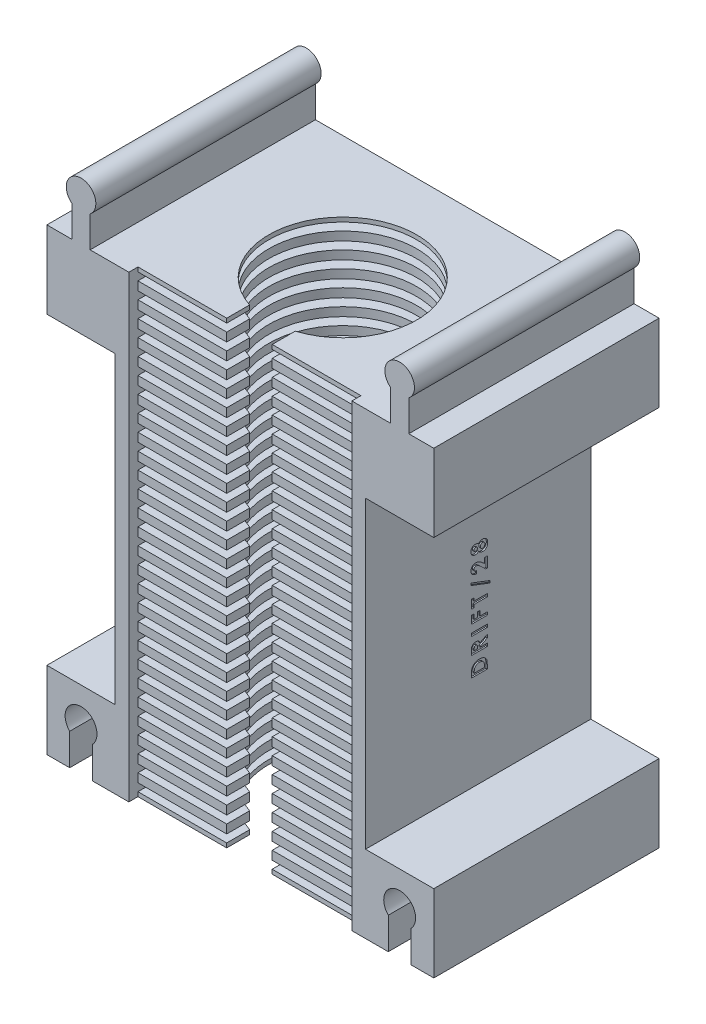
SolidWorks part; units mm, degrees
ref_plane "Plan de face" through (0, 0, 0) normal (0, 0, 1) x (1, 0, 0)
ref_plane "Plan de dessus" through (0, 0, 0) normal (0, 1, 0) x (1, 0, 0)
ref_plane "Plan de droite" through (0, 0, 0) normal (1, 0, 0) x (0, 0, -1)
sketch "Esquisse1" plane through (0, 0, 0) normal (0, 0, 1) x (1, 0, 0)
  line L1 (-20.1477, 24.3067) -> (34.8523, 24.3067)
  line L2 (-20.1477, 24.3067) -> (-20.1477, -85.1933)
  line L3 (-20.1477, -85.1933) -> (34.8523, -85.1933)
  line L4 (34.8523, 24.3067) -> (34.8523, -85.1933)
  dimension "D1" = 55
  dimension "D2" = 109.5
extrude "Boss.-Extru.2" add sketch "Esquisse1" along normal blind 49.5
sketch "Esquisse6" plane through (0, 0, 49.5) normal (0, 0, 1) x (1, 0, 0)
  line L0 (-20.1477, -85.1933) -> (34.8523, -85.1933) construction
  line L1 (-17.1477, 17.5067) -> (31.8523, 17.5067)
  line L2 (-17.1477, 17.5067) -> (-17.1477, -85.1933)
  line L3 (-17.1477, -85.1933) -> (31.8523, -85.1933)
  line L4 (31.8523, 17.5067) -> (31.8523, -85.1933)
  line L5 (-20.1477, 24.3067) -> (-20.1477, -85.1933) construction
  dimension "D1" = 49
  dimension "D2" = 3
  dimension "D3" = 102.7
extrude "Enlèv. mat.-Extru.2" cut sketch "Esquisse6" against normal blind 47
sketch "Esquisse7" plane through (0, 0, 2.5) normal (0, 0, 1) x (1, 0, 0)
  line L0 (31.8523, -85.1933) -> (31.8523, 17.5067) construction
  line L1 (-17.1477, -85.1933) -> (31.8523, -85.1933)
  line L2 (-17.1477, -85.1933) -> (-17.1477, -83.2933)
  line L3 (-17.1477, -83.2933) -> (31.8523, -83.2933)
  line L4 (31.8523, -85.1933) -> (31.8523, -83.2933)
  line L5 (-17.1477, -81.5933) -> (-17.1477, -79.6933)
  line L6 (-17.1477, -81.5933) -> (31.8523, -81.5933)
  line L7 (31.8523, -81.5933) -> (31.8523, -79.6933)
  line L8 (-17.1477, -79.6933) -> (31.8523, -79.6933)
  line L9 (-17.1477, -77.9933) -> (-17.1477, -76.0933)
  line L10 (-17.1477, -77.9933) -> (31.8523, -77.9933)
  line L11 (31.8523, -77.9933) -> (31.8523, -76.0933)
  line L12 (-17.1477, -76.0933) -> (31.8523, -76.0933)
  line L13 (-17.1477, -74.3933) -> (-17.1477, -72.4933)
  line L14 (-17.1477, -74.3933) -> (31.8523, -74.3933)
  line L15 (31.8523, -74.3933) -> (31.8523, -72.4933)
  line L16 (-17.1477, -72.4933) -> (31.8523, -72.4933)
  line L17 (-17.1477, -70.7933) -> (-17.1477, -68.8933)
  line L18 (-17.1477, -70.7933) -> (31.8523, -70.7933)
  line L19 (31.8523, -70.7933) -> (31.8523, -68.8933)
  line L20 (-17.1477, -68.8933) -> (31.8523, -68.8933)
  line L21 (-17.1477, -67.1933) -> (-17.1477, -65.2933)
  line L22 (-17.1477, -67.1933) -> (31.8523, -67.1933)
  line L23 (31.8523, -67.1933) -> (31.8523, -65.2933)
  line L24 (-17.1477, -65.2933) -> (31.8523, -65.2933)
  line L25 (-17.1477, -63.5933) -> (-17.1477, -61.6933)
  line L26 (-17.1477, -63.5933) -> (31.8523, -63.5933)
  line L27 (31.8523, -63.5933) -> (31.8523, -61.6933)
  line L28 (-17.1477, -61.6933) -> (31.8523, -61.6933)
  line L29 (-17.1477, -59.9933) -> (-17.1477, -58.0933)
  line L30 (-17.1477, -59.9933) -> (31.8523, -59.9933)
  line L31 (31.8523, -59.9933) -> (31.8523, -58.0933)
  line L32 (-17.1477, -58.0933) -> (31.8523, -58.0933)
  line L33 (-17.1477, -56.3933) -> (-17.1477, -54.4933)
  line L34 (-17.1477, -56.3933) -> (31.8523, -56.3933)
  line L35 (31.8523, -56.3933) -> (31.8523, -54.4933)
  line L36 (-17.1477, -54.4933) -> (31.8523, -54.4933)
  line L37 (-17.1477, -52.7933) -> (-17.1477, -50.8933)
  line L38 (-17.1477, -52.7933) -> (31.8523, -52.7933)
  line L39 (31.8523, -52.7933) -> (31.8523, -50.8933)
  line L40 (-17.1477, -50.8933) -> (31.8523, -50.8933)
  line L41 (-17.1477, -49.1933) -> (-17.1477, -47.2933)
  line L42 (-17.1477, -49.1933) -> (31.8523, -49.1933)
  line L43 (31.8523, -49.1933) -> (31.8523, -47.2933)
  line L44 (-17.1477, -47.2933) -> (31.8523, -47.2933)
  line L45 (-17.1477, -45.5933) -> (-17.1477, -43.6933)
  line L46 (-17.1477, -45.5933) -> (31.8523, -45.5933)
  line L47 (31.8523, -45.5933) -> (31.8523, -43.6933)
  line L48 (-17.1477, -43.6933) -> (31.8523, -43.6933)
  line L49 (-17.1477, -41.9933) -> (-17.1477, -40.0933)
  line L50 (-17.1477, -41.9933) -> (31.8523, -41.9933)
  line L51 (31.8523, -41.9933) -> (31.8523, -40.0933)
  line L52 (-17.1477, -40.0933) -> (31.8523, -40.0933)
  line L53 (-17.1477, -38.3933) -> (-17.1477, -36.4933)
  line L54 (-17.1477, -38.3933) -> (31.8523, -38.3933)
  line L55 (31.8523, -38.3933) -> (31.8523, -36.4933)
  line L56 (-17.1477, -36.4933) -> (31.8523, -36.4933)
  line L57 (-17.1477, -34.7933) -> (-17.1477, -32.8933)
  line L58 (-17.1477, -34.7933) -> (31.8523, -34.7933)
  line L59 (31.8523, -34.7933) -> (31.8523, -32.8933)
  line L60 (-17.1477, -32.8933) -> (31.8523, -32.8933)
  line L61 (-17.1477, -31.1933) -> (-17.1477, -29.2933)
  line L62 (-17.1477, -31.1933) -> (31.8523, -31.1933)
  line L63 (31.8523, -31.1933) -> (31.8523, -29.2933)
  line L64 (-17.1477, -29.2933) -> (31.8523, -29.2933)
  line L65 (-17.1477, -27.5933) -> (-17.1477, -25.6933)
  line L66 (-17.1477, -27.5933) -> (31.8523, -27.5933)
  line L67 (31.8523, -27.5933) -> (31.8523, -25.6933)
  line L68 (-17.1477, -25.6933) -> (31.8523, -25.6933)
  line L69 (-17.1477, -23.9933) -> (-17.1477, -22.0933)
  line L70 (-17.1477, -23.9933) -> (31.8523, -23.9933)
  line L71 (31.8523, -23.9933) -> (31.8523, -22.0933)
  line L72 (-17.1477, -22.0933) -> (31.8523, -22.0933)
  line L73 (-17.1477, -20.3933) -> (-17.1477, -18.4933)
  line L74 (-17.1477, -20.3933) -> (31.8523, -20.3933)
  line L75 (31.8523, -20.3933) -> (31.8523, -18.4933)
  line L76 (-17.1477, -18.4933) -> (31.8523, -18.4933)
  line L77 (-17.1477, -16.7933) -> (-17.1477, -14.8933)
  line L78 (-17.1477, -16.7933) -> (31.8523, -16.7933)
  line L79 (31.8523, -16.7933) -> (31.8523, -14.8933)
  line L80 (-17.1477, -14.8933) -> (31.8523, -14.8933)
  line L81 (-17.1477, -13.1933) -> (-17.1477, -11.2933)
  line L82 (-17.1477, -13.1933) -> (31.8523, -13.1933)
  line L83 (31.8523, -13.1933) -> (31.8523, -11.2933)
  line L84 (-17.1477, -11.2933) -> (31.8523, -11.2933)
  line L85 (-17.1477, -9.5933) -> (-17.1477, -7.6933)
  line L86 (-17.1477, -9.5933) -> (31.8523, -9.5933)
  line L87 (31.8523, -9.5933) -> (31.8523, -7.6933)
  line L88 (-17.1477, -7.6933) -> (31.8523, -7.6933)
  line L89 (-17.1477, -5.9933) -> (-17.1477, -4.0933)
  line L90 (-17.1477, -5.9933) -> (31.8523, -5.9933)
  line L91 (31.8523, -5.9933) -> (31.8523, -4.0933)
  line L92 (-17.1477, -4.0933) -> (31.8523, -4.0933)
  line L93 (-17.1477, -2.3933) -> (-17.1477, -0.4933)
  line L94 (-17.1477, -2.3933) -> (31.8523, -2.3933)
  line L95 (31.8523, -2.3933) -> (31.8523, -0.4933)
  line L96 (-17.1477, -0.4933) -> (31.8523, -0.4933)
  line L97 (-17.1477, 1.2067) -> (-17.1477, 3.1067)
  line L98 (-17.1477, 1.2067) -> (31.8523, 1.2067)
  line L99 (31.8523, 1.2067) -> (31.8523, 3.1067)
  line L100 (-17.1477, 3.1067) -> (31.8523, 3.1067)
  line L101 (-17.1477, 4.8067) -> (-17.1477, 6.7067)
  line L102 (-17.1477, 4.8067) -> (31.8523, 4.8067)
  line L103 (31.8523, 4.8067) -> (31.8523, 6.7067)
  line L104 (-17.1477, 6.7067) -> (31.8523, 6.7067)
  line L105 (-17.1477, 8.4067) -> (-17.1477, 10.3067)
  line L106 (-17.1477, 8.4067) -> (31.8523, 8.4067)
  line L107 (31.8523, 8.4067) -> (31.8523, 10.3067)
  line L108 (-17.1477, 10.3067) -> (31.8523, 10.3067)
  line L109 (-17.1477, 12.0067) -> (-17.1477, 13.9067)
  line L110 (-17.1477, 12.0067) -> (31.8523, 12.0067)
  line L111 (31.8523, 12.0067) -> (31.8523, 13.9067)
  line L112 (-17.1477, 13.9067) -> (31.8523, 13.9067)
  line L113 (-17.1477, 15.6067) -> (-17.1477, 17.5067)
  line L114 (-17.1477, 15.6067) -> (31.8523, 15.6067)
  line L115 (31.8523, 15.6067) -> (31.8523, 17.5067)
  line L116 (-17.1477, 17.5067) -> (31.8523, 17.5067)
  dimension "D1" = 1.9
  dimension "D2" = 29
extrude "Boss.-Extru.3" add sketch "Esquisse7" along normal blind 45
sketch "Esquisse8" plane through (0, -85.1933, 0) normal (0, -1, 0) x (1, 0, 0)
  line L0 (-17.1477, 47.5) -> (-17.1477, 49.5) construction
  line L1 (-20.1477, 49.5) -> (-20.1477, 0) construction
  circle A0 centre (7.3523, 27) radius 16.25
  point P4 (-17.1477, 48.5)
  dimension "D1" = 32.5
  dimension "D2" = 21.5
  dimension "D3" = 27.5
extrude "Enlèv. mat.-Extru.4" cut sketch "Esquisse8" against normal through all
sketch "Esquisse9" plane through (0, -85.1933, 0) normal (0, -1, 0) x (1, 0, 0)
  line L0 (2.3523, 47.5) -> (2.3523, 42.4616)
  line L1 (-17.1477, 47.5) -> (31.8523, 47.5) construction
  line L2 (12.3523, 47.5) -> (12.3523, 42.4616)
  line L3 (2.3523, 47.5) -> (12.3523, 47.5)
  line L4 (-20.1477, 49.5) -> (-20.1477, 0) construction
  line L5 (2.3523, 42.4616) -> (12.3523, 42.4616)
  circle A0 centre (7.3523, 27) radius 16.25 construction
  dimension "D1" = 10
  dimension "D2" = 22.5
extrude "Enlèv. mat.-Extru.5" cut sketch "Esquisse9" against normal through all
sketch "Esquisse11" plane through (0, 0, 49.5) normal (0, 0, 1) x (1, 0, 0)
  line L1 (34.8523, -85.1933) -> (49.8523, -85.1933)
  line L2 (34.8523, -85.1933) -> (34.8523, -67.2433)
  line L3 (34.8523, -67.2433) -> (49.8523, -67.2433)
  line L4 (49.8523, -85.1933) -> (49.8523, -67.2433)
  dimension "D1" = 15
  dimension "D2" = 17.95
extrude "Boss.-Extru.4" add sketch "Esquisse11" against normal up to surface (49.5 mm away) up to face at (7.3523, -30.4433, 0)
sketch "Esquisse12" plane through (0, 0, 49.5) normal (0, 0, 1) x (1, 0, 0)
  line L1 (-20.1477, -85.1933) -> (-35.1477, -85.1933)
  line L2 (-20.1477, -85.1933) -> (-20.1477, -67.2433)
  line L3 (-20.1477, -67.2433) -> (-35.1477, -67.2433)
  line L4 (-35.1477, -85.1933) -> (-35.1477, -67.2433)
  dimension "D1" = 17.95
  dimension "D2" = 15
extrude "Boss.-Extru.5" add sketch "Esquisse12" against normal up to surface (49.5 mm away) up to face at (21.5189, -42.71, 0)
sketch "Esquisse13" plane through (0, 0, 49.5) normal (0, 0, 1) x (1, 0, 0)
  line L0 (44.8523, -85.1933) -> (44.8523, -77.2933)
  line L1 (31.8523, -85.1933) -> (49.8523, -85.1933) construction
  line L2 (39.8523, -77.2933) -> (39.8523, -85.1933)
  line L3 (39.8523, -85.1933) -> (44.8523, -85.1933)
  line L4 (49.8523, -85.1933) -> (49.8523, -67.2433) construction
  line L5 (7.3523, -85.1933) -> (7.3523, -67.1933) construction
  line L6 (-8.8977, -85.1933) -> (23.6023, -85.1933) construction
  line L7 (-8.8977, -67.1933) -> (23.6023, -67.1933) construction
  line L8 (-30.1477, -85.1933) -> (-30.1477, -77.2933)
  line L9 (-25.1477, -85.1933) -> (-30.1477, -85.1933)
  line L10 (-25.1477, -77.2933) -> (-25.1477, -85.1933)
  arc A0 (39.8523, -77.2933) -> (44.8523, -77.2933) centre (42.3523, -74.8438) cw
  arc A1 (-25.1477, -77.2933) -> (-30.1477, -77.2933) centre (-27.6477, -74.8438) ccw
  dimension "D4" = 3.5
  dimension "D1" = 5
  dimension "D2" = 5
  dimension "D3" = 2.5
  dimension "D5" = 7.9
extrude "Enlèv. mat.-Extru.6" cut sketch "Esquisse13" against normal through all
sketch "Esquisse16" plane through (0, -85.1933, 0) normal (0, -1, 0) x (1, 0, 0)
  line L0 (49.8523, 49.5) -> (44.8523, 49.5) construction
  line L1 (44.8523, 49.5) -> (44.8523, 0) construction
  line L2 (44.8523, 0) -> (49.8523, 0) construction
  line L3 (49.8523, 0) -> (49.8523, 49.5) construction
  line L4 (-35.1477, 0) -> (-30.1477, 0) construction
  line L5 (-30.1477, 0) -> (-30.1477, 49.5) construction
  line L6 (-30.1477, 49.5) -> (-35.1477, 49.5) construction
  line L7 (-35.1477, 49.5) -> (-35.1477, 0) construction
  line L8 (-25.1477, 0) -> (39.8523, 0) construction
  line L9 (39.8523, 0) -> (39.8523, 49.5) construction
  line L10 (39.8523, 49.5) -> (31.8523, 49.5) construction
  line L11 (31.8523, 49.5) -> (31.8523, 47.5) construction
  line L12 (31.8523, 47.5) -> (12.3523, 47.5) construction
  line L13 (12.3523, 47.5) -> (12.3523, 42.4616) construction
  line L14 (2.3523, 42.4616) -> (2.3523, 47.5) construction
  line L15 (2.3523, 47.5) -> (-17.1477, 47.5) construction
  line L16 (-17.1477, 47.5) -> (-17.1477, 49.5) construction
  line L17 (-17.1477, 49.5) -> (-25.1477, 49.5) construction
  line L18 (-25.1477, 49.5) -> (-25.1477, 0) construction
  line L19 (49.8523, 49.5) -> (44.8523, 49.5)
  line L20 (44.8523, 49.5) -> (44.8523, 0)
  line L21 (44.8523, 0) -> (49.8523, 0)
  line L22 (49.8523, 0) -> (49.8523, 49.5)
  line L23 (-35.1477, 0) -> (-30.1477, 0)
  line L24 (-30.1477, 0) -> (-30.1477, 49.5)
  line L25 (-30.1477, 49.5) -> (-35.1477, 49.5)
  line L26 (-35.1477, 49.5) -> (-35.1477, 0)
  line L27 (-25.1477, 0) -> (39.8523, 0)
  line L28 (39.8523, 0) -> (39.8523, 49.5)
  line L29 (39.8523, 49.5) -> (31.8523, 49.5)
  line L30 (31.8523, 49.5) -> (31.8523, 47.5)
  line L31 (31.8523, 47.5) -> (12.3523, 47.5)
  line L32 (12.3523, 47.5) -> (12.3523, 42.4616)
  line L33 (2.3523, 42.4616) -> (2.3523, 47.5)
  line L34 (2.3523, 47.5) -> (-17.1477, 47.5)
  line L35 (-17.1477, 47.5) -> (-17.1477, 49.5)
  line L36 (-17.1477, 49.5) -> (-25.1477, 49.5)
  line L37 (-25.1477, 49.5) -> (-25.1477, 0)
  arc A0 (2.3523, 42.4616) -> (12.3523, 42.4616) centre (7.3523, 27) ccw construction
  arc A1 (2.3523, 42.4616) -> (12.3523, 42.4616) centre (7.3523, 27) ccw
extrude "Enlèv. mat.-Extru.9" cut sketch "Esquisse16" against normal blind 0.95
sketch "Esquisse17" plane through (0, 24.3067, 0) normal (0, 1, 0) x (1, 0, 0)
  line L4 (34.8523, 0) -> (-20.1477, 0)
  line L5 (-20.1477, 0) -> (-20.1477, -49.5)
  line L6 (-20.1477, -49.5) -> (34.8523, -49.5)
  line L7 (34.8523, -49.5) -> (34.8523, 0)
  line L8 (34.8523, 0) -> (-20.1477, 0)
  line L9 (-20.1477, 0) -> (-20.1477, -49.5)
  line L10 (-20.1477, -49.5) -> (34.8523, -49.5)
  line L11 (34.8523, -49.5) -> (34.8523, 0)
  dimension "D1" = 0
extrude "Enlèv. mat.-Extru.10" cut sketch "Esquisse17" against normal blind 7.75
sketch "Esquisse18" plane through (0, 0, 49.5) normal (0, 0, 1) x (1, 0, 0)
  line L1 (-20.1477, 16.5567) -> (-35.1477, 16.5567)
  line L2 (-20.1477, 16.5567) -> (-20.1477, -0.4433)
  line L3 (-20.1477, -0.4433) -> (-35.1477, -0.4433)
  line L4 (-35.1477, 16.5567) -> (-35.1477, -0.4433)
  line L5 (34.8523, 16.5567) -> (49.8523, 16.5567)
  line L6 (34.8523, 16.5567) -> (34.8523, -0.4433)
  line L7 (34.8523, -0.4433) -> (49.8523, -0.4433)
  line L8 (49.8523, 16.5567) -> (49.8523, -0.4433)
  dimension "D1" = 17
  dimension "D2" = 15
  dimension "D3" = 15
  dimension "D4" = 17
extrude "Boss.-Extru.6" add sketch "Esquisse18" against normal up to surface (49.5 mm away) up to face at (7.3523, -64.9121, 0)
sketch "Esquisse19" plane through (0, 0, 49.5) normal (0, 0, 1) x (1, 0, 0)
  line L0 (-25.6477, 16.5567) -> (-25.6477, 23.3967)
  line L1 (-35.1477, 16.5567) -> (-17.1477, 16.5567) construction
  line L2 (-25.6477, 16.5567) -> (-29.6477, 16.5567)
  line L3 (-29.6477, 16.5567) -> (-29.6477, 23.3967)
  line L4 (-35.1477, 16.5567) -> (-35.1477, -0.4433) construction
  line L5 (7.3523, 30.7544) -> (7.3523, 24.9911) construction
  line L6 (49.8523, -0.4433) -> (49.8523, 16.5567) construction
  line L7 (40.3523, 16.5567) -> (44.3523, 16.5567)
  line L8 (44.3523, 16.5567) -> (44.3523, 23.3967)
  line L9 (40.3523, 16.5567) -> (40.3523, 23.3967)
  arc A0 (-29.6477, 23.3967) -> (-25.6477, 23.3967) centre (-27.6477, 25.9584) cw
  arc A1 (44.3523, 23.3967) -> (40.3523, 23.3967) centre (42.3523, 25.9584) ccw
  dimension "D3" = 3.25
  dimension "D1" = 6.84
  dimension "D2" = 6.84
  dimension "D4" = 4
  dimension "D5" = 5.5
  dimension "D6" = 42.5
extrude "Boss.-Extru.7" add sketch "Esquisse19" against normal up to surface (49.5 mm away) up to face at (7.3523, -52.0184, 0)
sketch "Esquisse20" plane through (34.8523, 0, 0) normal (1, 0, 0) x (0, 0, -1)
  line L0 (-22.75, -67.2433) -> (-22.75, -0.4433) construction
  line L1 (0, -67.2433) -> (-49.5, -67.2433) construction
  line L2 (0, -0.4433) -> (-49.5, -0.4433) construction
  line L3 (-49.5, -67.2433) -> (-49.5, -0.4433) construction
  text T0 "<b>DRIFT/28</b>" font "Century Gothic" height 3.5
  dimension "D1" = 26.75
extrude "Enlèv. mat.-Extru.11" cut sketch "Esquisse20" against normal blind 0.3
